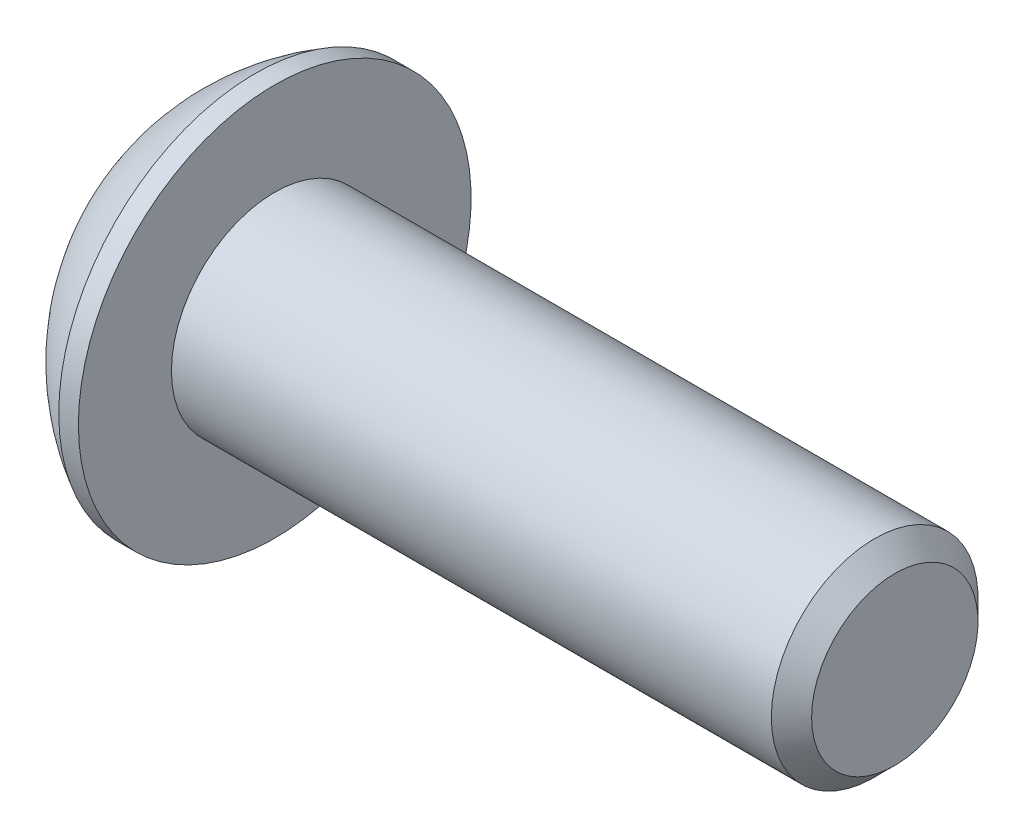
SolidWorks part; units mm, degrees
ref_plane "Front Plane" through (0, 0, 0) normal (0, 0, 1) x (1, 0, 0)
ref_plane "Top Plane" through (0, 0, 0) normal (0, 1, 0) x (1, 0, 0)
ref_plane "Right Plane" through (0, 0, 0) normal (1, 0, 0) x (0, 0, -1)
sketch "Sketch1" plane through (0, 0, 0) normal (0, 0, 1) x (1, 0, 0)
  line L0 (14.2, 0) -> (14.2, 1.61)
  line L1 (13.81, 2) -> (2.2, 2)
  line L2 (2.2, 2) -> (2.2, 3.8)
  line L3 (2.2, 3.8) -> (1.82, 3.8)
  line L5 (-2.0247, 0) -> (15.4994, 0) construction
  line L7 (14.2, 0) -> (0, 0)
  line L9 (0, 0) -> (0, 1.9)
  line L10 (14.2, 1.61) -> (13.81, 2)
  arc A1 (0, 1.9) -> (1.82, 3.8) centre (3.8853, 0) cw
  dimension "D2" = 4.325
  dimension "D1" = 135
  dimension "Head_side_ht" = 0.38
  dimension "D3" = 14.2
  dimension "D4" = 11.61
  dimension "D5" = 1.8
  dimension "D6" = 1.9
revolve "Revolve1" add sketch "Sketch1" angle 360 about L5
sketch "Sketch2" plane through (0, 0, 0) normal (-1, 0, 0) x (0, 0, 1)
  line L1 (0.7027, -1.261) -> (1.4434, -0.0219)
  line L2 (1.4434, -0.0219) -> (0.7407, 1.239)
  line L3 (0.7407, 1.239) -> (-0.7027, 1.261)
  line L4 (-0.7027, 1.261) -> (-1.4434, 0.0219)
  line L5 (-1.4434, 0.0219) -> (-0.7407, -1.239)
  line L6 (-0.7407, -1.239) -> (0.7027, -1.261)
  circle A0 centre (0, 0) radius 1.2501 construction
  dimension "D1" = 1.4434
extrude "Cut-Extrude1" cut sketch "Sketch2" against normal blind 1.3
